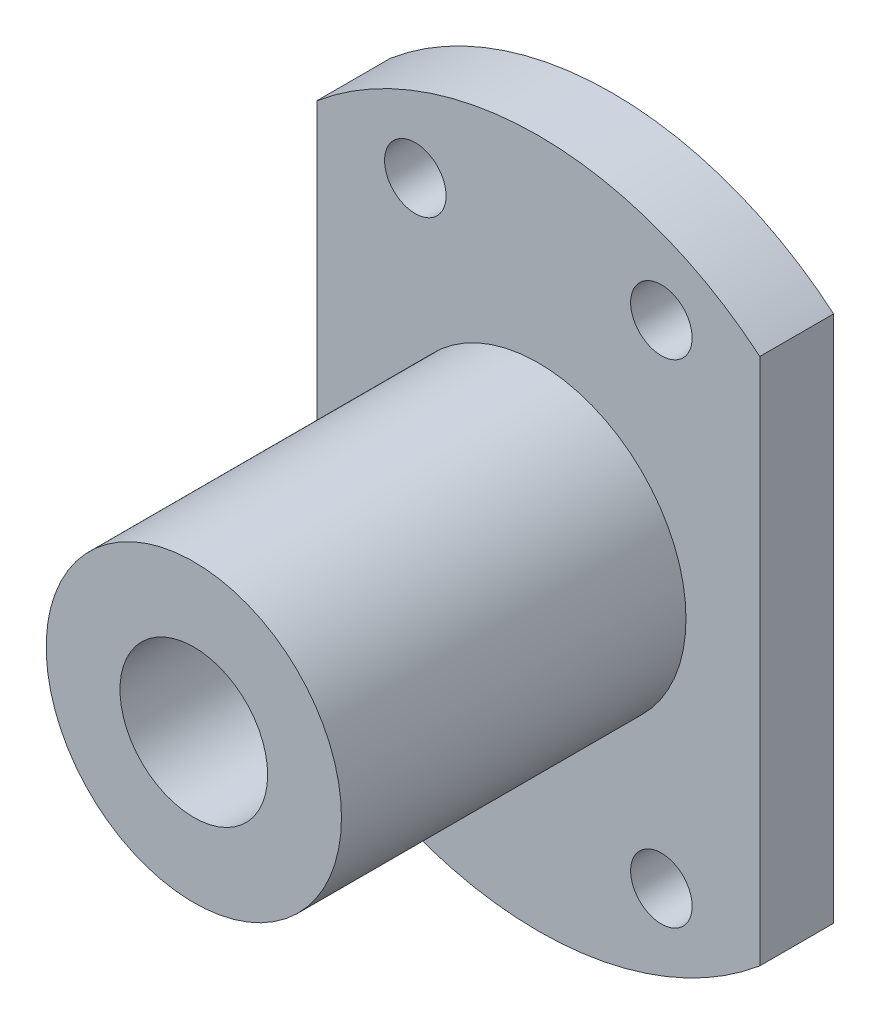
SolidWorks part; units mm, degrees
ref_plane "Front Plane" through (0, 0, 0) normal (0, 0, 1) x (1, 0, 0)
ref_plane "Top Plane" through (0, 0, 0) normal (0, 1, 0) x (1, 0, 0)
ref_plane "Right Plane" through (0, 0, 0) normal (1, 0, 0) x (0, 0, -1)
sketch "Sketch1" plane through (0, 0, 0) normal (0, 0, 1) x (1, 0, 0)
  line L0 (-9, 10.7238) -> (-9, -10.7238)
  line L1 (9, 10.7238) -> (9, -10.7238)
  line L2 (-9, 0) -> (9, 0) construction
  line L3 (-5, 10) -> (5, -10) construction
  line L4 (-5, -10) -> (5, 10) construction
  arc A0 (9, 10.7238) -> (-9, 10.7238) centre (0, 0) ccw
  arc A1 (-9, -10.7238) -> (9, -10.7238) centre (0, 0) ccw
  circle A2 centre (0, 0) radius 3
  circle A3 centre (-5, 10) radius 1.25
  circle A4 centre (5, 10) radius 1.25
  circle A5 centre (-5, -10) radius 1.25
  circle A6 centre (5, -10) radius 1.25
  point P7 (0, 0)
  point P18 (0, 0)
  dimension "D2" = 14
  dimension "D3" = 6
  dimension "D6" = 2.5
  dimension "D1" = 18
  dimension "D4" = 20
  dimension "D5" = 10
extrude "Boss-Extrude1" add sketch "Sketch1" along normal blind 3
sketch "Sketch2" plane through (0, 0, 3) normal (0, 0, 1) x (1, 0, 0)
  circle A0 centre (0, 0) radius 6
  circle A1 centre (0, 0) radius 3
  circle A2 centre (0, 0) radius 3 construction
  dimension "D1" = 12
extrude "LinearBallSupport" add sketch "Sketch2" along normal blind 14
